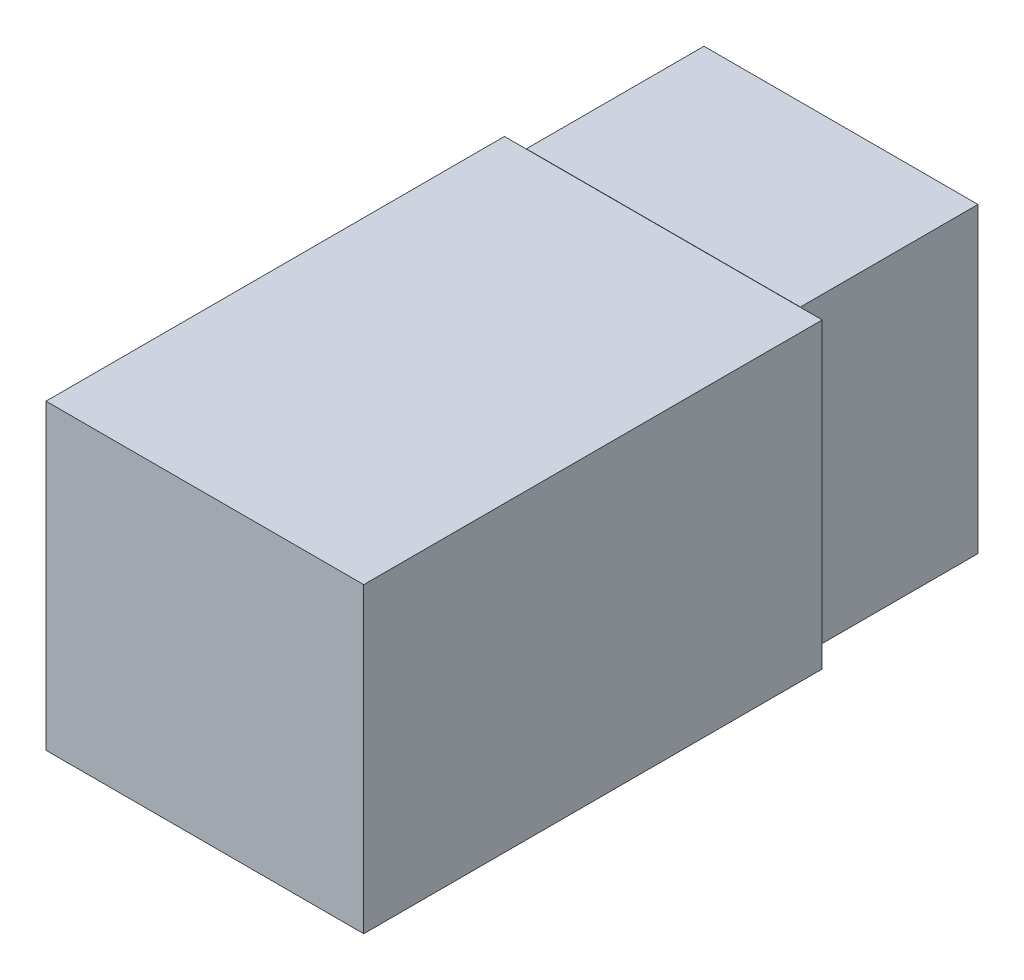
SolidWorks part; units mm, degrees
ref_plane "Front Plane" through (0, 0, 0) normal (0, 0, 1) x (1, 0, 0)
ref_plane "Top Plane" through (0, 0, 0) normal (0, 1, 0) x (1, 0, 0)
ref_plane "Right Plane" through (0, 0, 0) normal (1, 0, 0) x (0, 0, -1)
sketch "Sketch1" plane through (0, 0, 0) normal (0, 0, 1) x (1, 0, 0)
  line L1 (0, 0) -> (14.5, 0)
  line L2 (0, 0) -> (0, 16)
  line L3 (0, 16) -> (14.5, 16)
  line L4 (14.5, 0) -> (14.5, 16)
extrude "Boss-Extrude1" add sketch "Sketch1" along normal blind 9.4
sketch "Sketch4" plane through (0, 0, 9.4) normal (0, 0, 1) x (1, 0, 0)
  line L1 (-1.1575, 15.9863) -> (15.6564, 15.9863)
  line L2 (-1.1575, 15.9863) -> (-1.1575, -0.0137)
  line L3 (-1.1575, -0.0137) -> (15.6564, -0.0137)
  line L4 (15.6564, 15.9863) -> (15.6564, -0.0137)
extrude "Boss-Extrude3" add sketch "Sketch4" along normal blind 24.26
shell "Shell1" thickness 1.3
